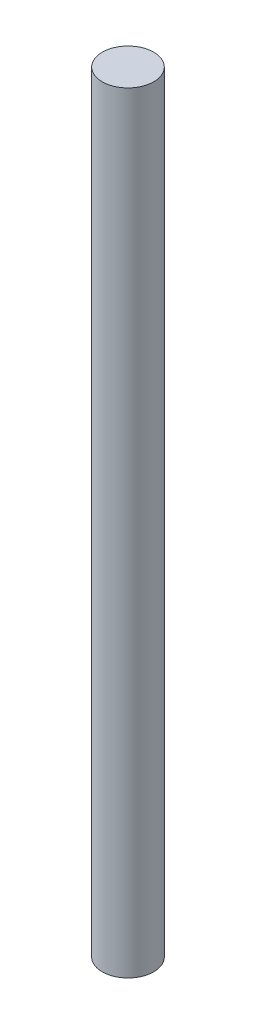
SolidWorks part; units mm, degrees
ref_plane "Front" through (0, 0, 0) normal (0, 0, 1) x (1, 0, 0)
ref_plane "Top" through (0, 0, 0) normal (0, 1, 0) x (1, 0, 0)
ref_plane "Right" through (0, 0, 0) normal (1, 0, 0) x (0, 0, -1)
sketch "Sketch1" plane through (0, 0, 0) normal (0, 1, 0) x (1, 0, 0)
  circle A0 centre (0, 0) radius 2.5
  dimension "D1" = 5
extrude "Boss-Extrude1" add sketch "Sketch1" along normal blind 75
